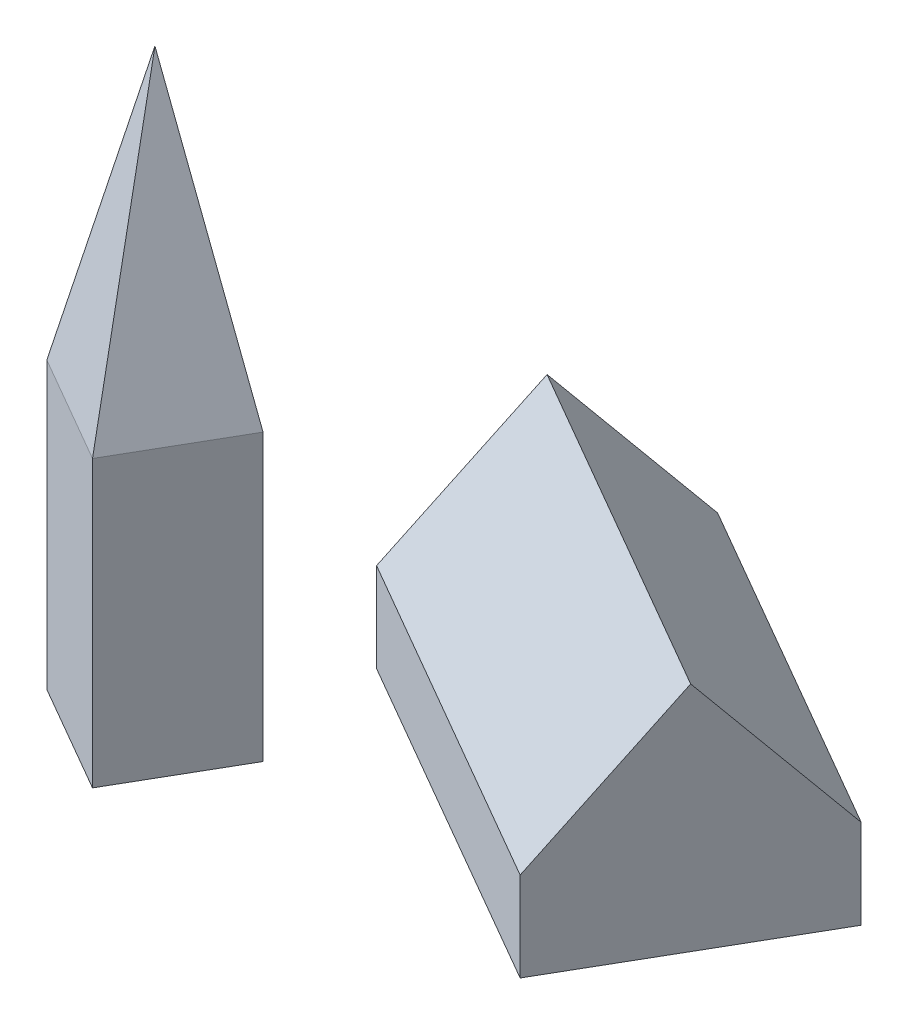
SolidWorks part; units mm, degrees
ref_plane "Front" through (0, 0, 0) normal (0, 0, 1) x (1, 0, 0)
ref_plane "Top" through (0, 0, 0) normal (0, 1, 0) x (1, 0, 0)
ref_plane "Right" through (0, 0, 0) normal (1, 0, 0) x (0, 0, -1)
sketch "Sketch1" plane through (0, 0, 0) normal (0, 1, 0) x (1, 0, 0)
  line L0 (0, 0) -> (95.2628, -55)
  line L1 (95.2628, -55) -> (60.2628, -115.6218)
  line L2 (60.2628, -115.6218) -> (-35, -60.6218)
  line L3 (-35, -60.6218) -> (0, 0)
  line L4 (60.2628, -115.6218) -> (85.1494, -115.6218) construction
  dimension "D1" = 60
  dimension "D2" = 110
  dimension "D3" = 70
extrude "Extrude1" add sketch "Sketch1" along normal blind 25
sketch "Sketch2" plane through (95.2628, 0, 55) normal (0.866, 0, 0.5) x (0.5, 0, -0.866)
  line L0 (-70, 25) -> (0, 25)
  line L1 (0, 25) -> (-35, 65)
  line L2 (-35, 65) -> (-70, 25)
  dimension "D1" = 40
extrude "Extrude2" add sketch "Sketch2" against normal blind 110
sketch "Sketch3" plane through (0, 0, 0) normal (0, 1, 0) x (1, 0, 0)
  line L0 (-58.6603, -81.6025) -> (-28.3494, -99.1025)
  line L1 (-28.3494, -99.1025) -> (-45.8494, -129.4134)
  line L2 (-45.8494, -129.4134) -> (-76.1603, -111.9134)
  line L3 (-76.1603, -111.9134) -> (-58.6603, -81.6025)
  line L6 (-35, -60.6218) -> (60.2628, -115.6218) construction
  line L7 (-17.5, -30.3109) -> (-35, -60.6218) construction
  dimension "D1" = 35
  dimension "D2" = 10
  dimension "D3" = 30
extrude "Extrude3" add sketch "Sketch3" along normal blind 80
sketch "Sketch4" plane through (0, 80, 0) normal (0, 1, 0) x (-1, 0, 0)
  line L0 (58.6603, 81.6025) -> (28.3494, 99.1025)
  line L1 (28.3494, 99.1025) -> (45.8494, 129.4134)
  line L2 (45.8494, 129.4134) -> (76.1603, 111.9134)
  line L3 (76.1603, 111.9134) -> (58.6603, 81.6025)
  line L4 (58.6603, 81.6025) -> (45.8494, 129.4134) construction
  point P4 (52.2548, 105.508)
ref_plane "Plane1" through (0, 0, 105.508) normal (0, 0, 1) x (1, 0, 0)
sketch "Sketch5" plane through (0, 0, 105.508) normal (0, 0, 1) x (1, 0, 0)
  point P0 (-52.2548, 165)
  dimension "D1" = 85
loft "Loft1" add profiles "Sketch5", "Sketch4"
